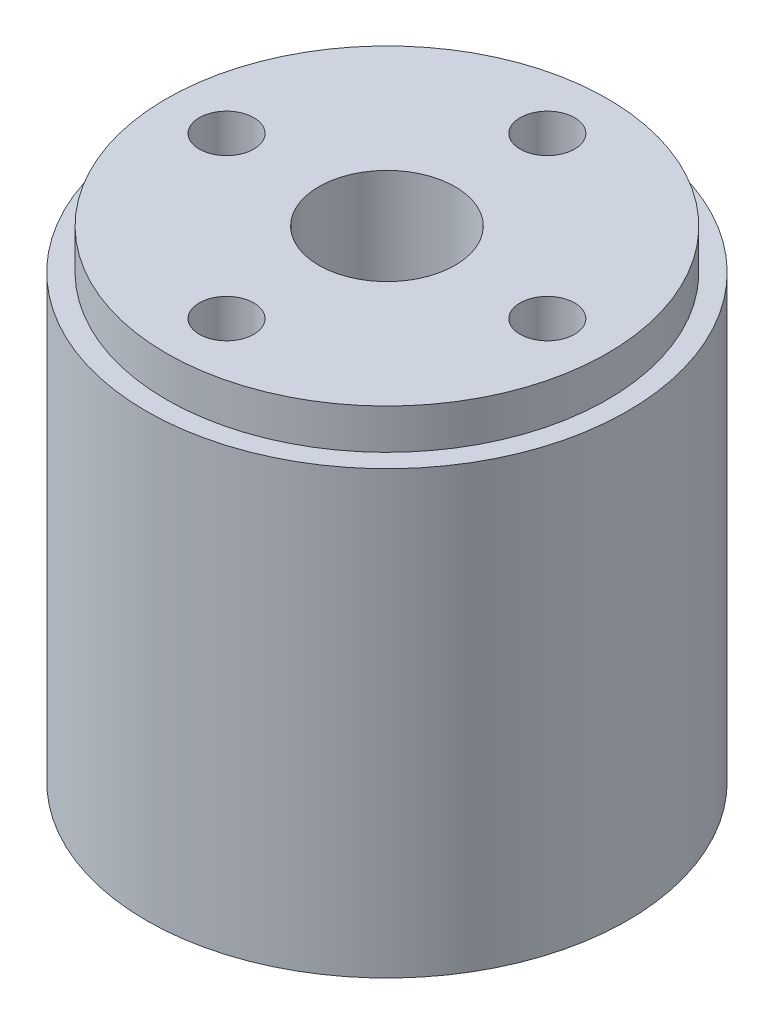
SolidWorks part; units mm, degrees
ref_plane "Front Plane" through (0, 0, 0) normal (0, 0, 1) x (1, 0, 0)
ref_plane "Top Plane" through (0, 0, 0) normal (0, 1, 0) x (1, 0, 0)
ref_plane "Right Plane" through (0, 0, 0) normal (1, 0, 0) x (0, 0, -1)
sketch "Sketch1" plane through (0, 0, 0) normal (0, 1, 0) x (1, 0, 0)
  line L0 (0, 0) -> (0, 41406.0778) construction
  line L1 (0, 0) -> (-41406.0778, 0) construction
  circle A0 centre (0, 0) radius 30
  circle A1 centre (0, 0) radius 8.5
  circle A2 centre (-20, 0) radius 3.4
  circle A3 centre (0, 20) radius 3.4
  circle A4 centre (20, 0) radius 3.4
  circle A5 centre (0, -20) radius 3.4
  point P10 (0, 0)
  point P11 (0, 0)
  point P12 (0, 0)
  point P19 (0, 0)
  dimension "D1" = 60
  dimension "D2" = 17
  dimension "D3" = 6.8
  dimension "D4" = 20
  dimension "D5" = 4
extrude "Boss-Extrude1" add sketch "Sketch1" along normal blind 60
sketch "Sketch3" plane through (0, 60, 0) normal (0, 1, 0) x (1, 0, 0)
  circle A0 centre (0, 0) radius 27.5
  circle A1 centre (0, 0) radius 30
  dimension "D1" = 55
extrude "Cut-Extrude1" cut sketch "Sketch3" against normal blind 5
chamfer "Chamfer1" distance 5 angle 45 1 edges at (0, 0, 8.5)
